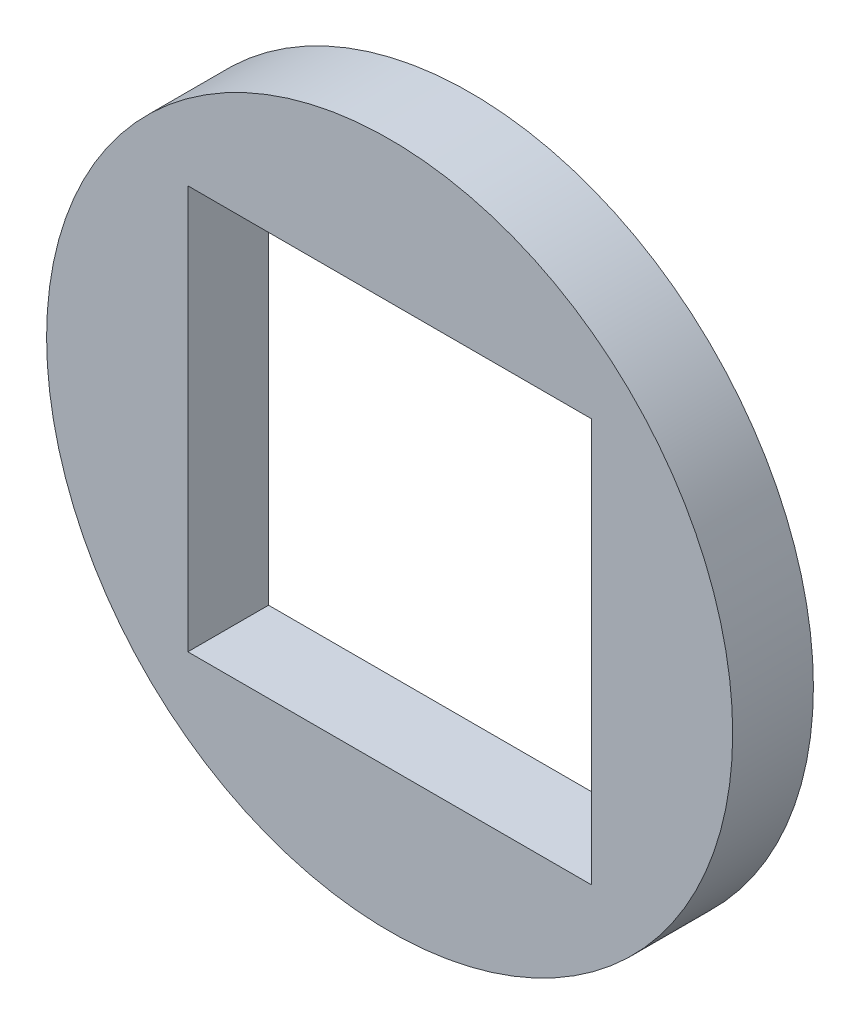
SolidWorks part; units mm, degrees
material "Acrylic (Medium-high impact)"
ref_plane "Front Plane" through (0, 0, 0) normal (0, 0, 1) x (1, 0, 0)
ref_plane "Top Plane" through (0, 0, 0) normal (0, 1, 0) x (1, 0, 0)
ref_plane "Right Plane" through (0, 0, 0) normal (1, 0, 0) x (0, 0, -1)
sketch "Model" plane through (0, 0, 0) normal (0, 0, 1) x (1, 0, 0)
  line L1 (-5, -5) -> (5, -5)
  line L2 (-5, -5) -> (-5, 5)
  line L3 (-5, 5) -> (5, 5)
  line L4 (5, -5) -> (5, 5)
  line L5 (-5, -5) -> (5, 5) construction
  line L6 (-5, 5) -> (5, -5) construction
  circle A0 centre (0, 0) radius 8.5
  dimension "D1" = 17
  dimension "D2" = 10
  dimension "D3" = 10
extrude "Boss-Extrude1" add sketch "Model" along normal blind 2
